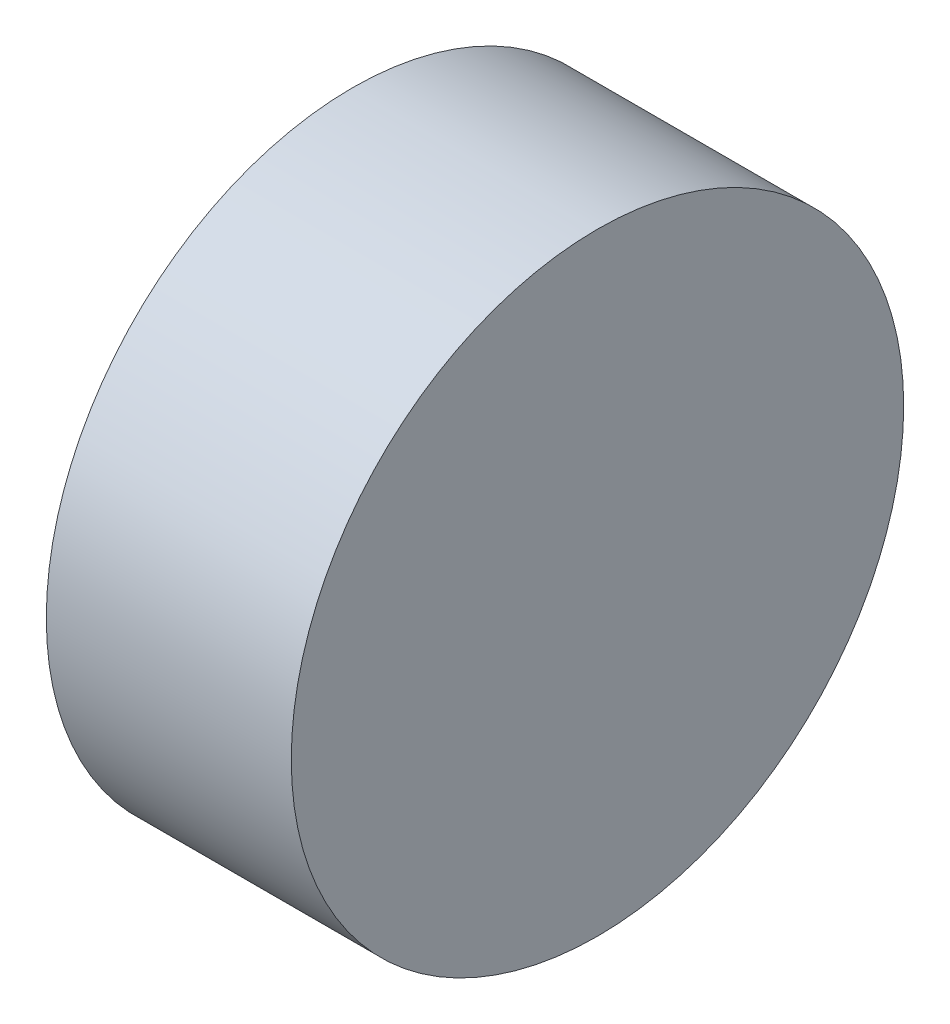
SolidWorks part; units mm, degrees
ref_plane "前视基准面" through (0, 0, 0) normal (0, 0, 1) x (1, 0, 0)
ref_plane "上视基准面" through (0, 0, 0) normal (0, 1, 0) x (1, 0, 0)
ref_plane "右视基准面" through (0, 0, 0) normal (1, 0, 0) x (0, 0, -1)
sketch "草图1" plane through (0, 0, 0) normal (0, 0, 1) x (1, 0, 0)
  line L0 (127.0004, 38.6466) -> (139.6266, 38.6466) construction
  line L1 (130.064, 38.6466) -> (130.064, 46.1466)
  line L2 (136.064, 38.6466) -> (136.064, 46.1466)
  line L3 (130.064, 38.6466) -> (136.064, 38.6466)
  line L5 (130.064, 46.1466) -> (136.064, 46.1466)
revolve "旋转1" add sketch "草图1" angle 360 about L0
